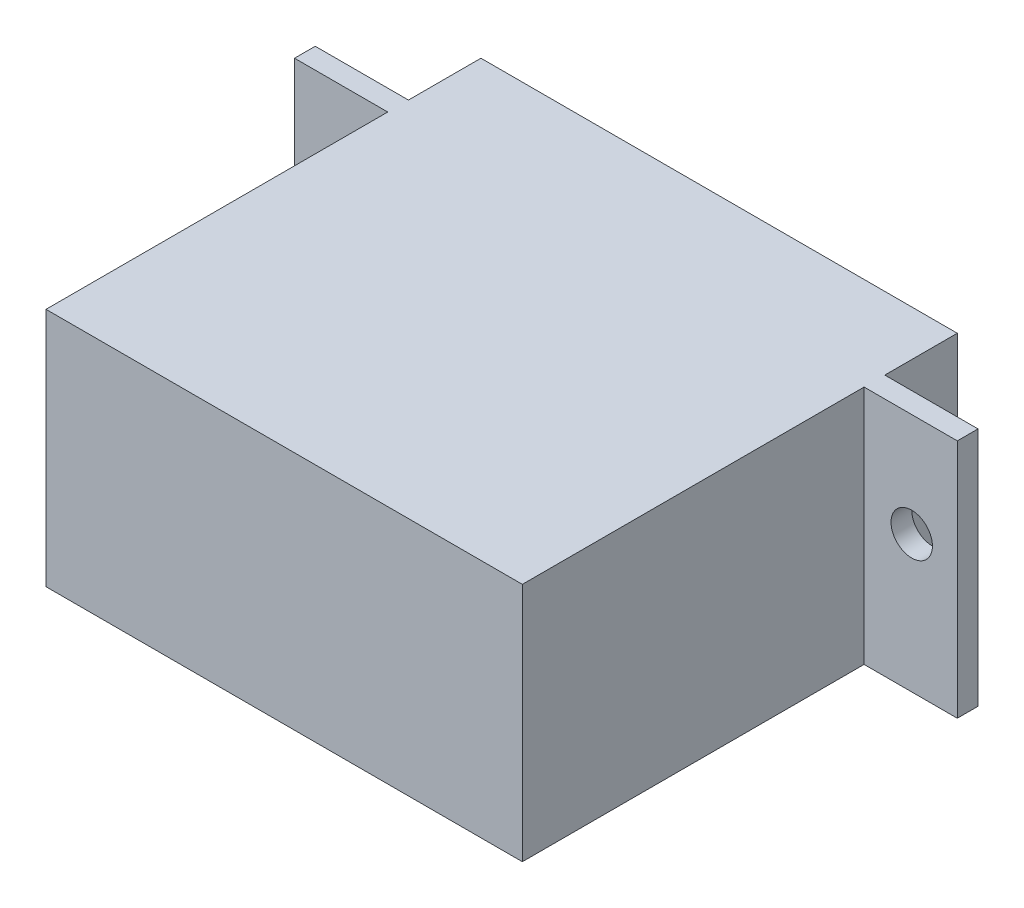
SolidWorks part; units mm, degrees
ref_plane "Front" through (0, 0, 0) normal (0, 0, 1) x (1, 0, 0)
ref_plane "Top" through (0, 0, 0) normal (0, 1, 0) x (1, 0, 0)
ref_plane "Right" through (0, 0, 0) normal (1, 0, 0) x (0, 0, -1)
sketch "Sketch1" plane through (0, 0, 0) normal (0, 1, 0) x (1, 0, 0)
  line L1 (-11.5, 10.5) -> (11.5, 10.5)
  line L2 (-11.5, 10.5) -> (-11.5, -10.5)
  line L3 (-11.5, -10.5) -> (11.5, -10.5)
  line L4 (11.5, 10.5) -> (11.5, -10.5)
  line L5 (-11.5, 10.5) -> (11.5, -10.5) construction
  line L6 (-11.5, -10.5) -> (11.5, 10.5) construction
  point P0 (0, 0)
  dimension "D1" = 21
  dimension "D2" = 23
extrude "Boss-Extrude1" add sketch "Sketch1" along normal blind 11.6
sketch "Sketch2" plane through (11.5, 0, 0) normal (1, 0, 0) x (0, 0, -1)
  line L0 (7, 0) -> (-10.5, 0) construction
  line L1 (-10.5, 0) -> (10.5, 0) construction
  line L2 (7, 0) -> (7, 11.6)
  line L3 (-10.5, 11.6) -> (10.5, 11.6) construction
  line L4 (7, 11.6) -> (6, 11.6)
  line L5 (6, 11.6) -> (6, 0)
  line L6 (6, 0) -> (7, 0)
  dimension "D1" = 17.5
  dimension "D2" = 1
extrude "Boss-Extrude2" add sketch "Sketch2" along normal blind 4.5
mirror "Mirror1" about plane through (0, 0, 0) normal (1, 0, 0) of "Boss-Extrude2"
sketch "Sketch3" plane through (0, 0, -10.5) normal (0, 0, -1) x (-1, 0, 0)
  line L0 (-11.5, 5.8) -> (-5.5, 5.8) construction
  line L1 (-11.5, 11.6) -> (-11.5, 0) construction
  circle A0 centre (-5.5, 5.8) radius 2
  circle A1 centre (-5.5, 5.8) radius 0.6
  dimension "D2" = 4
  dimension "D3" = 1.2
  dimension "D1" = 6
extrude "Boss-Extrude3" add sketch "Sketch3" along normal blind 3.7
sketch "Sketch4" plane through (0, 0, -7) normal (0, 0, -1) x (-1, 0, 0)
  line L0 (-13.8, 11.6) -> (-13.8, 6.6) construction
  line L2 (0, 0) -> (0, 11.6) construction
  line L3 (-11.5, 11.6) -> (11.5, 11.6) construction
  line L4 (0, 11.6) -> (-13.8, 11.6) construction
  circle A0 centre (-13.8, 6.6) radius 1
  circle A1 centre (13.8, 6.6) radius 1
  dimension "D2" = 2
  dimension "D1" = 5
  dimension "D3" = 13.8
extrude "Cut-Extrude1" cut sketch "Sketch4" against normal blind 5
equation "\"servo_long\"=23"
equation "\"D2@Sketch1\"=\"servo_long\""
equation "\"servo_width\"=21"
equation "\"D1@Sketch1\"=\"servo_width\""
equation "\"servo_height\"=11.6"
equation "\"D1@Boss-Extrude1\"=\"servo_height\""
